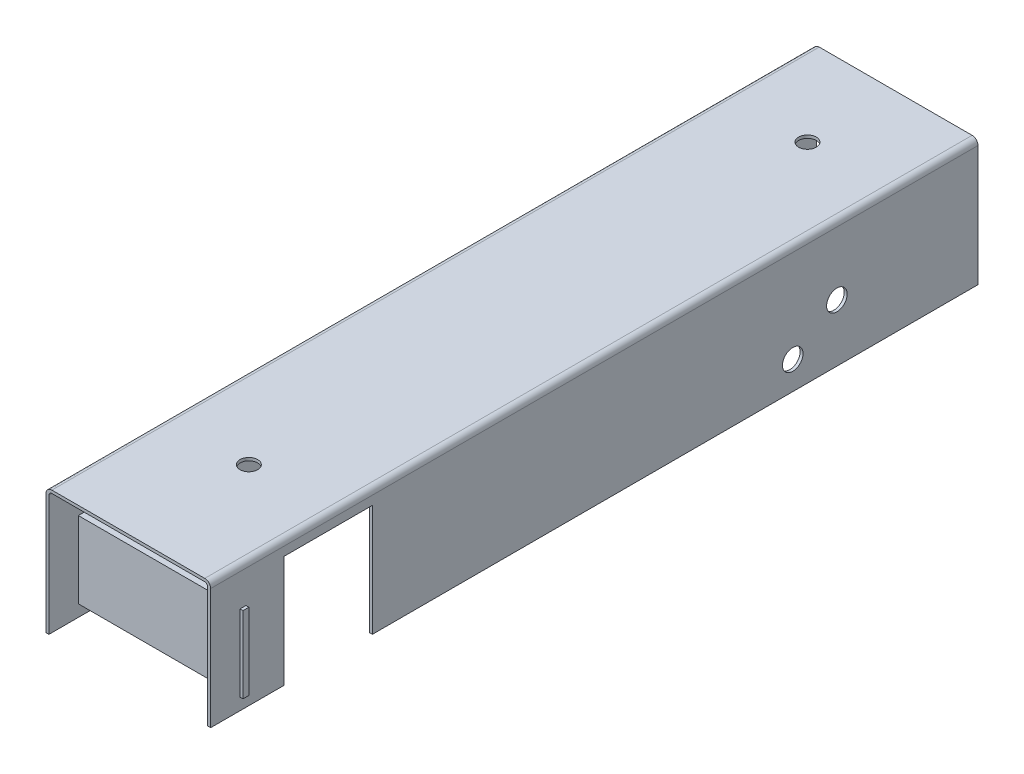
SolidWorks part; units mm, degrees
ref_plane "Płaszczyzna przednia" through (0, 0, 0) normal (0, 0, 1) x (1, 0, 0)
ref_plane "Płaszczyzna górna" through (0, 0, 0) normal (0, 1, 0) x (1, 0, 0)
ref_plane "Płaszczyzna prawa" through (0, 0, 0) normal (1, 0, 0) x (0, 0, -1)
sketch "Sketch1" plane through (0, 0, 0) normal (0, 0, 1) x (1, 0, 0)
  line L0 (26.6977, -20.5) -> (27, -20.5)
  line L1 (-28, 21.5) -> (28, 21.5)
  line L2 (-28, 21.5) -> (-28, -21.5)
  line L4 (28, 21.5) -> (28, -21.5)
  line L5 (-28, 21.5) -> (28, -21.5) construction
  line L6 (-28, -21.5) -> (28, 21.5) construction
  line L7 (-27, 20.5) -> (27, 20.5)
  line L8 (-27, 20.5) -> (-27, -20.5)
  line L9 (-27, -20.5) -> (-26.6977, -20.5)
  line L10 (27, 20.5) -> (27, -20.5)
  line L11 (-27, 20.5) -> (27, -20.5) construction
  line L12 (-27, -20.5) -> (27, 20.5) construction
  line L13 (-28, -21.5) -> (-27, -21.5)
  line L14 (-27, -21.5) -> (-27, -20.5)
  line L15 (28, -21.5) -> (27, -21.5)
  line L16 (27, -21.5) -> (27, -20.5)
  point P0 (0, 0)
  point P6 (0, 0)
  dimension "D1" = 56
  dimension "D2" = 43
  dimension "D3" = 54
  dimension "D4" = 41
extrude "Boss-Extrude1" add sketch "Sketch1" along normal blind 261 contours L16 L15 L4 L1 L2 L13 L14 L8 L7 L10
fillet "Fillet1" radius 2 2 edges at (-28, 21.5, 130.5) (28, 21.5, 130.5)
fillet "Fillet2" radius 1 2 edges at (27, 20.5, 130.5) (-27, 20.5, 130.5)
sketch "Sketch2" plane through (-27, 0, 0) normal (1, 0, 0) x (0, 0, -1)
  line L0 (-251, -21.5) -> (-251, 19.5) construction
  line L1 (-261, -21.5) -> (0, -21.5) construction
  line L2 (0, 19.5) -> (-261, 19.5) construction
  line L3 (-261, 19.5) -> (-261, -21.5) construction
  line L4 (-251, -17.5) -> (-261, -17.5) construction
  line L10 (-251, -17.5) -> (-249, -17.5)
  line L11 (-251, -17.5) -> (-251, 8.5)
  line L12 (-251, 8.5) -> (-249, 8.5)
  line L13 (-249, -17.5) -> (-249, 8.5)
  line L14 (-251, -17.5) -> (-249, 8.5) construction
  line L15 (-251, 8.5) -> (-249, -17.5) construction
  point P14 (-250, -4.5)
  dimension "D1" = 10
  dimension "D2" = 4
  dimension "D3" = 2
  dimension "D4" = 26
extrude "Boss-Extrude2" add sketch "Sketch2" along normal blind 56 and the other way blind 2
sketch "Sketch3" plane through (0, 21.5, 0) normal (0, 1, 0) x (1, 0, 0)
  line L0 (0, 0) -> (0, -261) construction
  line L1 (-26, 0) -> (26, 0) construction
  line L2 (-26, -261) -> (26, -261) construction
  circle A0 centre (0, -30) radius 3
  circle A1 centre (0, -220) radius 3
  dimension "D1" = 30
  dimension "D2" = 41
extrude "Cut-Extrude1" cut sketch "Sketch3" against normal blind 11
sketch "Sketch4" plane through (28, 0, 0) normal (1, 0, 0) x (0, 0, -1)
  line L0 (-261, 21.5) -> (0, 21.5) construction
  line L1 (-236, 16.5) -> (-206, 16.5)
  line L2 (-236, 16.5) -> (-236, -23.5)
  line L3 (-236, -23.5) -> (-206, -23.5)
  line L4 (-206, 16.5) -> (-206, -23.5)
  line L5 (-236, 16.5) -> (-206, -23.5) construction
  line L6 (-236, -23.5) -> (-206, 16.5) construction
  line L7 (-261, 19.5) -> (-261, -21.5) construction
  point P4 (-221, -3.5)
  dimension "D1" = 40
  dimension "D2" = 30
  dimension "D3" = 5
  dimension "D4" = 25
extrude "Cut-Extrude2" cut sketch "Sketch4" against normal blind 10
sketch "Sketch5" plane through (28, 0, 0) normal (1, 0, 0) x (0, 0, -1)
  line L0 (-48, 21.5) -> (-48, -21.5) construction
  line L1 (-261, 21.5) -> (0, 21.5) construction
  line L2 (-206, -21.5) -> (0, -21.5) construction
  line L3 (-261, 19.5) -> (-261, -21.5) construction
  line L4 (-48, -2) -> (-63, -2) construction
  line L5 (-63, -2) -> (-63, -12) construction
  circle A0 centre (-48, -2) radius 3.5
  circle A1 centre (-63, -12) radius 3.5
  point P13 (-64.9536, -2)
  dimension "D1" = 213
  dimension "D2" = 23.5
extrude "Cut-Extrude3" cut sketch "Sketch5" against normal blind 76
